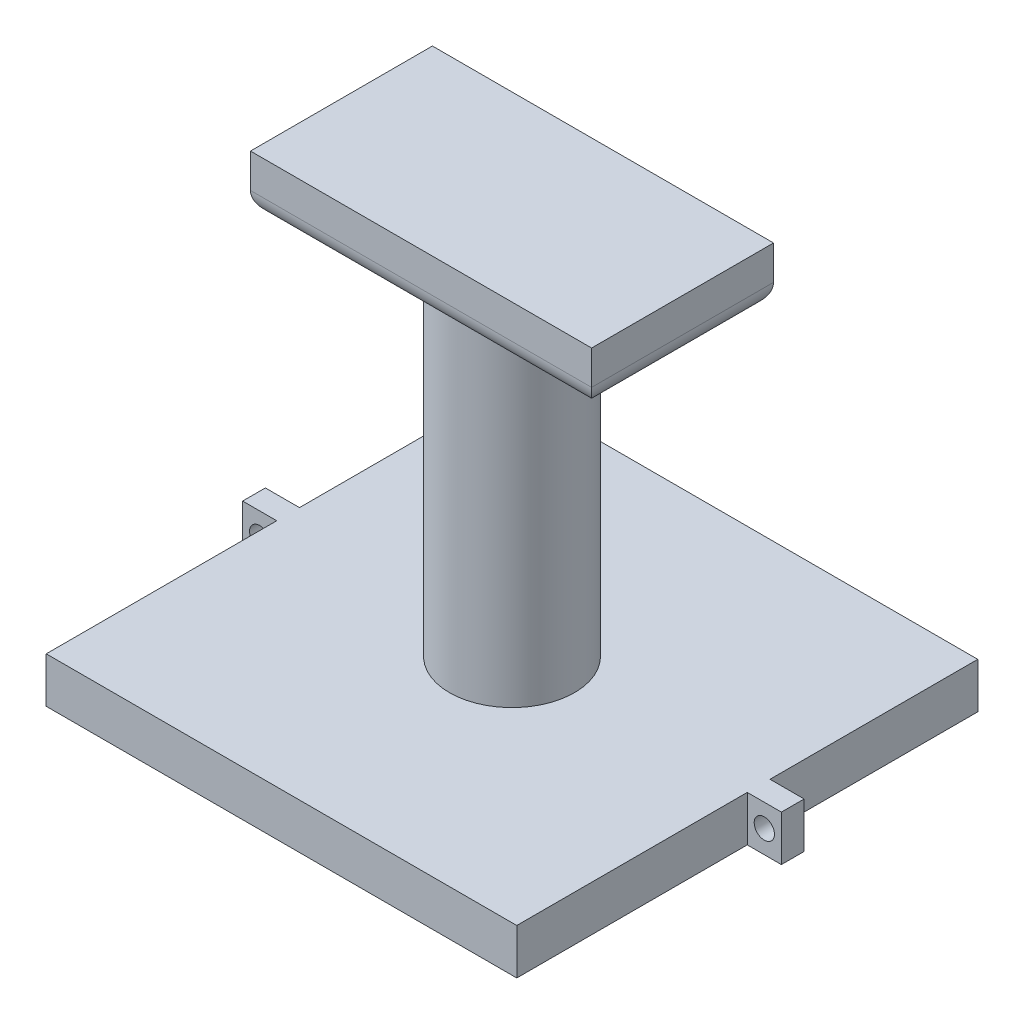
SolidWorks part; units mm, degrees
ref_plane "Front Plane" through (0, 0, 0) normal (0, 0, 1) x (1, 0, 0)
ref_plane "Top Plane" through (0, 0, 0) normal (0, 1, 0) x (1, 0, 0)
ref_plane "Right Plane" through (0, 0, 0) normal (1, 0, 0) x (0, 0, -1)
sketch "Sketch2" plane through (0, 0, 0) normal (0, 1, 0) x (1, 0, 0)
  line L0 (-26.2754, 25.743) -> (26.2754, 25.743)
  line L1 (-26.2754, 25.743) -> (-26.2754, -25.743)
  line L2 (26.2754, 25.743) -> (26.2754, -25.743)
  line L3 (-26.2754, -25.743) -> (26.2754, -25.743)
  line L12 (26.2754, 0) -> (26.2754, 2.54)
  line L13 (26.2754, 0) -> (30.0854, 0)
  line L14 (26.2754, 2.54) -> (30.0854, 2.54)
  line L15 (30.0854, 0) -> (30.0854, 2.54)
  line L16 (-26.2754, 2.54) -> (-26.2754, 0)
  line L17 (-26.2754, 2.54) -> (-30.0854, 2.54)
  line L18 (-26.2754, 0) -> (-30.0854, 0)
  line L19 (-30.0854, 2.54) -> (-30.0854, 0)
  dimension "D1" = 52.5507
  dimension "D2" = 51.486
  dimension "D3" = 25.743
  dimension "D4" = 25.743
  dimension "D5" = 2.54
  dimension "D6" = 3.81
  dimension "D7" = 26.2754
  dimension "D8" = 3.81
  dimension "D9" = 2.54
  dimension "D10" = 25.743
extrude "Boss-Extrude1" add sketch "Sketch2" along normal blind 5.08
sketch "Sketch3" plane through (0, 0, 0) normal (0, -1, 0) x (1, 0, 0)
  line L0 (23.7354, -23.203) -> (23.7354, 23.203)
  line L1 (23.7354, -23.203) -> (-23.7354, -23.203)
  line L2 (23.7354, 23.203) -> (-23.7354, 23.203)
  line L3 (-23.7354, -23.203) -> (-23.7354, 23.203)
  line L4 (-26.2754, 25.743) -> (26.2754, 25.743) construction
  line L5 (-26.2754, -25.743) -> (26.2754, -25.743) construction
  line L7 (-26.2754, -25.743) -> (-26.2754, -2.54) construction
  line L8 (26.2754, -25.743) -> (26.2754, -2.54) construction
  dimension "D1" = 2.54
  dimension "D2" = 2.54
  dimension "D3" = 2.54
  dimension "D4" = 2.54
extrude "Cut-Extrude1" cut sketch "Sketch3" against normal blind 3.81
ref_plane "Plane1" through (0, 0, 0) normal (0, 0, 1) x (1, 0, 0)
sketch "Sketch4" plane through (0, 0, 0) normal (0, 0, 1) x (1, 0, 0)
  line L0 (28.1804, 0) -> (28.1804, 5.08) construction
  line L1 (26.2754, 0) -> (30.0854, 0) construction
  line L2 (26.2754, 5.08) -> (30.0854, 5.08) construction
  line L3 (0, 5.08) -> (0, 0) construction
  line L4 (-26.2754, 5.08) -> (26.2754, 5.08) construction
  line L5 (-26.2754, 0) -> (26.2754, 0) construction
  circle A0 centre (28.1804, 2.54) radius 1.1303
  circle A1 centre (-28.1804, 2.54) radius 1.1303
  dimension "D1" = 2.2606
extrude "Cut-Extrude2" cut sketch "Sketch4" against normal blind 3.302
sketch "Sketch5" plane through (0, 5.08, 0) normal (0, 1, 0) x (1, 0, 0)
  circle A0 centre (0, 0) radius 5.08
  dimension "D1" = 10.16
extrude "Cut-Extrude3" cut sketch "Sketch5" against normal blind 1.9304
sketch "Sketch6" plane through (0, 5.08, 0) normal (0, 1, 0) x (1, 0, 0)
  circle A0 centre (0, 0) radius 6.985
  dimension "D1" = 13.97
extrude "Boss-Extrude2" add sketch "Sketch6" along normal blind 38.1
sketch "Sketch8" plane through (0, 43.18, 0) normal (0, 1, 0) x (1, 0, 0)
  circle A0 centre (0, 0) radius 5.08
  dimension "D1" = 10.16
extrude "Cut-Extrude4" cut sketch "Sketch8" against normal blind 38.1
sketch "Sketch7" plane through (0, 43.18, 0) normal (0, 1, 0) x (1, 0, 0)
  line L0 (-19.05, -10.16) -> (19.05, -10.16)
  line L1 (-19.05, -10.16) -> (-19.05, 10.16)
  line L2 (19.05, -10.16) -> (19.05, 10.16)
  line L3 (-19.05, 10.16) -> (19.05, 10.16)
  dimension "D1" = 19.05
  dimension "D2" = 38.1
  dimension "D3" = 10.16
  dimension "D4" = 20.32
extrude "Boss-Extrude3" add sketch "Sketch7" along normal blind 6.35
fillet "Fillet3" radius 2.54 4 edges at (19.05, 43.18, 0) (0, 43.18, -10.16) (-19.05, 43.18, 0) (0, 43.18, 10.16)
